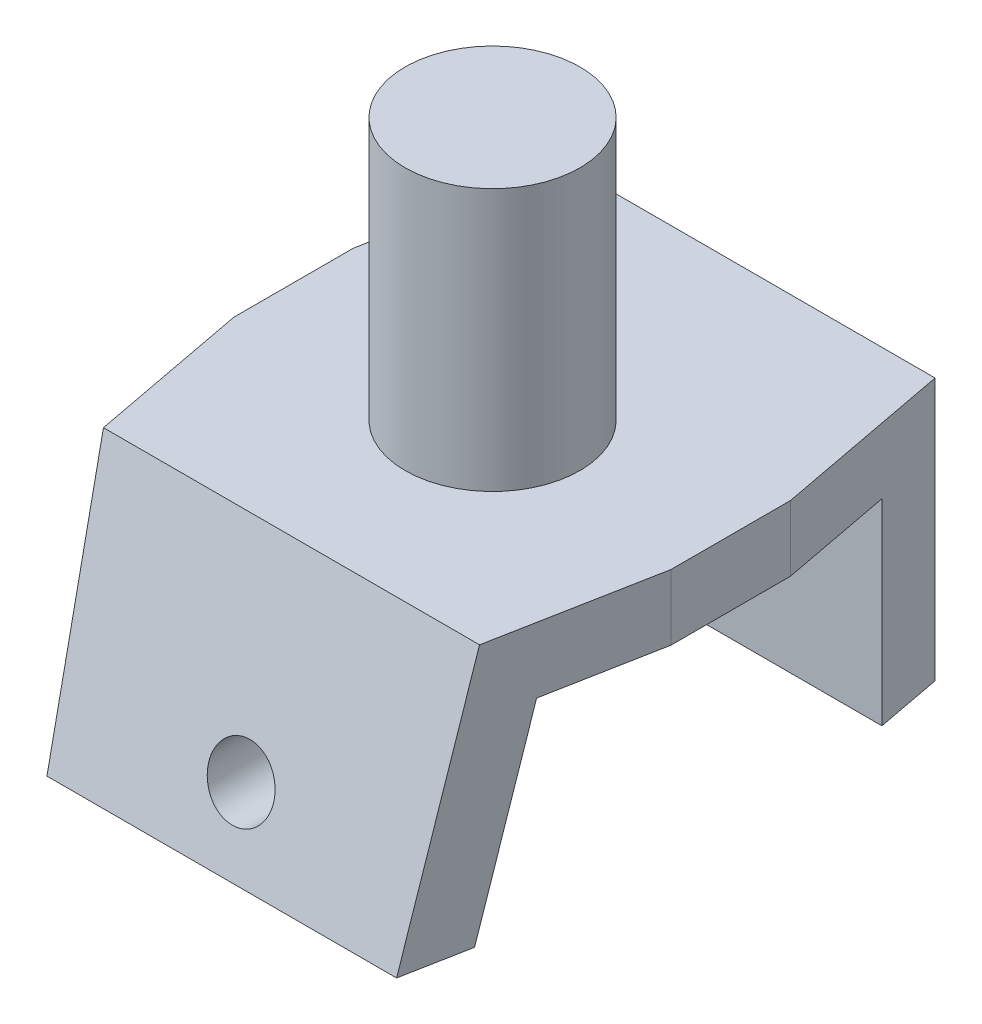
SolidWorks part; units mm, degrees
ref_plane "Front Plane" through (0, 0, 0) normal (0, 0, 1) x (1, 0, 0)
ref_plane "Top Plane" through (0, 0, 0) normal (0, 1, 0) x (1, 0, 0)
ref_plane "Right Plane" through (0, 0, 0) normal (1, 0, 0) x (0, 0, -1)
sketch "Sketch1" plane through (0, 0, 0) normal (1, 0, 0) x (0, 0, -1)
  line L0 (-51.4379, -28.7384) -> (-39.5, 15.8143)
  line L1 (-39.5, 15.8143) -> (39.5, 15.8143)
  line L2 (39.5, 15.8143) -> (39.5, -29.1857)
  line L3 (-51.4379, -28.7384) -> (-66.4379, -28.7384)
  line L4 (39.5, -29.1857) -> (54.5, -29.1857)
  line L5 (-66.4379, -28.7384) -> (-50.4808, 30.8143)
  line L6 (54.5, -29.1857) -> (54.5, 30.8143)
  line L7 (54.5, 30.8143) -> (-50.4808, 30.8143)
  dimension "D1" = 105
  dimension "D2" = 79
  dimension "D3" = 45
  dimension "D4" = 39.5
  dimension "D5" = 15
  dimension "D6" = 15
  dimension "D7" = 15
extrude "Boss-Extrude1" add sketch "Sketch1" along normal blind 100
sketch "Sketch2" plane through (0, 0, -54.5) normal (0, 0, -1) x (-1, 0, 0)
  line L0 (-100, 30.8143) -> (0, 30.8143) construction
  line L3 (-100, -29.1857) -> (-100, 30.8143) construction
  circle A0 centre (-50, -12.1857) radius 7.5
  dimension "D1" = 15
  dimension "D2" = 43
  dimension "D3" = 50
extrude "Cut-Extrude1" cut sketch "Sketch2" against normal blind 120
sketch "Sketch3" plane through (0, 30.8143, 0) normal (0, 1, 0) x (1, 0, 0)
  line L0 (10, -66.4379) -> (0, -13.684)
  line L1 (100, -66.4379) -> (0, -66.4379) construction
  line L2 (0, 54.5) -> (0, -50.4808) construction
  line L3 (0, -13.684) -> (-18.365, -13.684)
  line L4 (-18.365, -13.684) -> (-18.365, -72.1078)
  line L5 (-18.365, -72.1078) -> (10, -66.4379)
  line L6 (50, 63.0411) -> (50, -72.1078) construction
  line L7 (-38.5018, 0) -> (141.4622, 0) construction
  line L8 (-18.365, 72.1078) -> (10, 66.4379)
  line L9 (-18.365, 13.684) -> (-18.365, 72.1078)
  line L10 (0, 13.684) -> (-18.365, 13.684)
  line L11 (10, 66.4379) -> (0, 13.684)
  line L12 (90, 66.4379) -> (100, 13.684)
  line L13 (100, 13.684) -> (118.365, 13.684)
  line L14 (118.365, 13.684) -> (118.365, 72.1078)
  line L15 (118.365, 72.1078) -> (90, 66.4379)
  line L16 (118.365, -72.1078) -> (90, -66.4379)
  line L17 (118.365, -13.684) -> (118.365, -72.1078)
  line L18 (100, -13.684) -> (118.365, -13.684)
  line L19 (90, -66.4379) -> (100, -13.684)
  point P25 (118.365, -72.1078)
  dimension "D1" = 50
  dimension "D2" = 40
extrude "Cut-Extrude2" cut sketch "Sketch3" against normal blind 100
sketch "Sketch4" plane through (0, 30.8143, 0) normal (0, 1, 0) x (1, 0, 0)
  line L0 (100, 13.684) -> (100, -13.684) construction
  line L5 (93.0248, -50.4808) -> (6.9752, -50.4808) construction
  circle A0 centre (50, -4.4808) radius 20
  dimension "D1" = 40
  dimension "D2" = 50
  dimension "D3" = 46
extrude "Boss-Extrude2" add sketch "Sketch4" along normal blind 60
